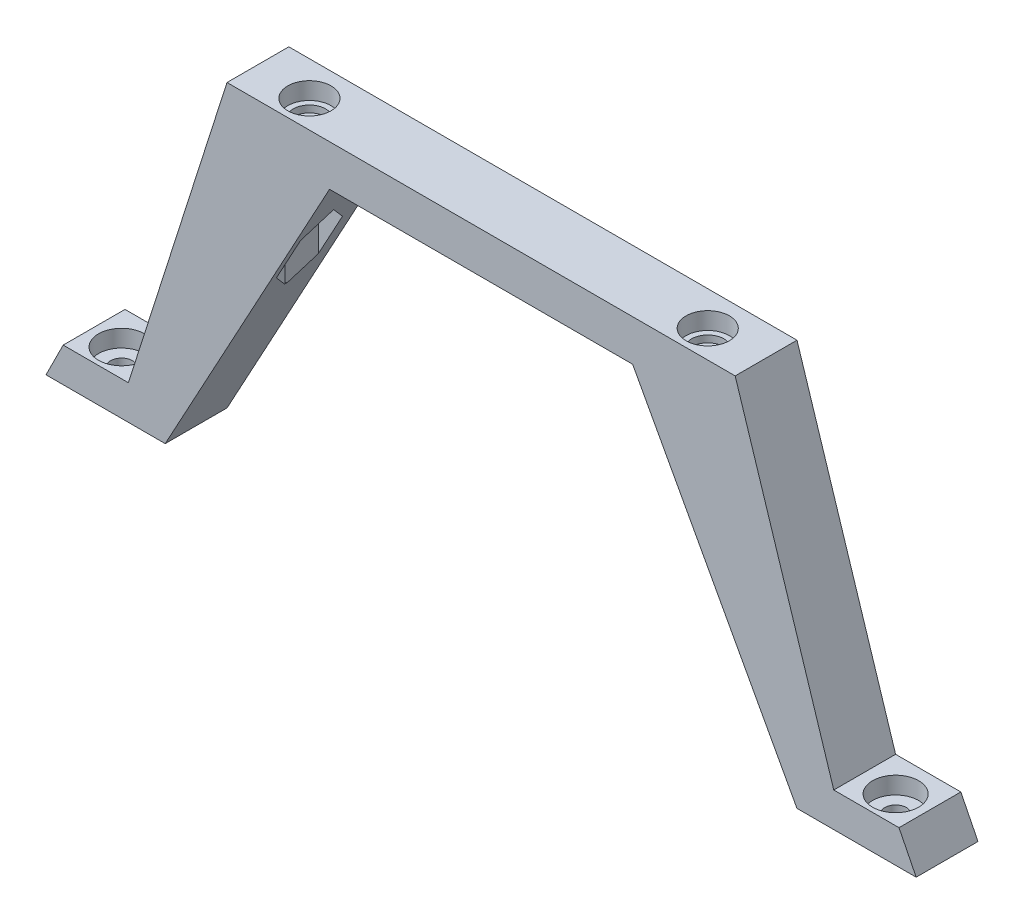
SolidWorks part; units mm, degrees
ref_plane "前视基准面" through (0, 0, 0) normal (0, 0, 1) x (1, 0, 0)
ref_plane "上视基准面" through (0, 0, 0) normal (0, 1, 0) x (1, 0, 0)
ref_plane "右视基准面" through (0, 0, 0) normal (1, 0, 0) x (0, 0, -1)
sketch "草图1" plane through (0, 0, 0) normal (0, 0, 1) x (1, 0, 0)
  line L0 (33.8113, 38.6957) -> (33.8113, 7.0528) construction
  line L1 (-3.1887, 13.0528) -> (33.8113, 13.0528)
  line L2 (-14.1858, -36.9913) -> (-12.1858, -36.9913)
  line L3 (-12.1858, -36.9913) -> (11.742, 7.0528)
  line L4 (33.8113, 13.0528) -> (33.8113, 7.0528)
  line L5 (15.602, 7.0528) -> (11.742, 7.0528)
  line L7 (33.8113, 7.0528) -> (15.602, 7.0528)
  line L10 (-17.5487, -31.9913) -> (-27.0458, -31.9913)
  line L12 (-27.0458, -31.9913) -> (-29.5458, -36.9913)
  line L13 (-29.5458, -36.9913) -> (-14.1858, -36.9913)
  line L16 (-17.5487, -31.9913) -> (-3.1887, 13.0528)
  point P0 (33.8113, 10.0528)
extrude "凸台-拉伸1" add sketch "草图1" along normal blind 10
ref_plane "基准面3" through (33.8113, 0, 0) normal (1, 0, 0) x (0, 0, -1)
mirror "镜向1" about plane through (33.8113, 13.0528, 10) normal (-1, 0, 0) of "凸台-拉伸1"
ref_plane "基准面1" through (0, 0, 5) normal (0, 0, 1) x (1, 0, 0)
sketch "草图5" plane through (0, 0, 5) normal (0, 0, 1) x (1, 0, 0)
  line L0 (33.8113, 20.2752) -> (33.8113, -16.9928) construction
  line L1 (70.8113, 13.0528) -> (-3.1887, 13.0528) construction
  line L2 (7.9613, 13.0528) -> (7.9613, 10.5528)
  line L3 (7.9613, 10.5528) -> (7.1613, 10.5528)
  line L4 (7.1613, 10.5528) -> (7.1613, 9.5528)
  line L5 (7.1613, 9.5528) -> (6.3613, 9.5528)
  line L6 (4.8113, 13.0528) -> (4.8113, 2.5746) construction
  line L7 (4.8113, 13.0528) -> (7.9613, 13.0528)
  line L8 (6.3613, 9.5528) -> (4.8113, 9.5528)
  line L9 (4.8113, 9.5528) -> (4.8113, 13.0528)
  point P2 (4.8113, 13.0528)
  point P3 (62.8113, 13.0274)
  point P6 (7.9613, 13.0528)
  point P13 (6.3613, 9.5528)
  dimension "D2" = 29
  dimension "D3" = 3.15
revolve "切除-旋转7" cut sketch "草图5" angle 360 about L9
sketch "草图7" plane through (0, 9.5528, 0) normal (0, 1, 0) x (1, 0, 0)
  circle A0 centre (4.8113, -5) radius 1.55
  dimension "D1" = 3.1
extrude "切除-拉伸1" cut sketch "草图7" against normal through all
ref_plane "基准面2" through (0, -11.9472, 0) normal (0, 1, 0) x (1, 0, 0)
sketch "草图8" plane through (0, -11.9472, 0) normal (0, 1, 0) x (1, 0, 0)
  line L1 (8.3331, -5) -> (6.5722, -1.95)
  line L2 (6.5722, -1.95) -> (3.0504, -1.95)
  line L3 (3.0504, -1.95) -> (1.2895, -5)
  line L4 (1.2895, -5) -> (3.0504, -8.05)
  line L5 (3.0504, -8.05) -> (6.5722, -8.05)
  line L6 (6.5722, -8.05) -> (8.3331, -5)
  circle A0 centre (4.8113, -5) radius 3.05 construction
  dimension "D1" = 6.1
extrude "切除-拉伸2" cut sketch "草图8" along normal blind 18.5
sketch "草图19" plane through (0, 13.0528, 0) normal (0, 1, 0) x (1, 0, 0)
  line L4 (97.1684, -10) -> (97.1684, -9.004)
  line L5 (97.1684, -9.004) -> (-29.5458, -9.004)
  line L6 (-29.5458, -9.004) -> (-29.5458, -10)
  line L17 (-29.5458, -10) -> (97.1684, -10)
extrude "切除-拉伸14" cut sketch "草图19" against normal through all
sketch "草图23" plane through (0, -31.9913, 0) normal (0, 1, 0) x (1, 0, 0)
  circle A1 centre (-22.5487, -5) radius 1.575
extrude "切除-拉伸16" cut sketch "草图23" against normal blind 10
sketch "草图24" plane through (0, -31.9913, 0) normal (0, 1, 0) x (1, 0, 0)
  circle A0 centre (-22.5487, -5) radius 3.35
extrude "切除-拉伸17" cut sketch "草图24" against normal blind 2.5
mirror "镜向3" about plane through (33.8113, 0, 0) normal (1, 0, 0) of "切除-拉伸1", "切除-拉伸17", "切除-拉伸16", "切除-拉伸2", "切除-旋转7"
